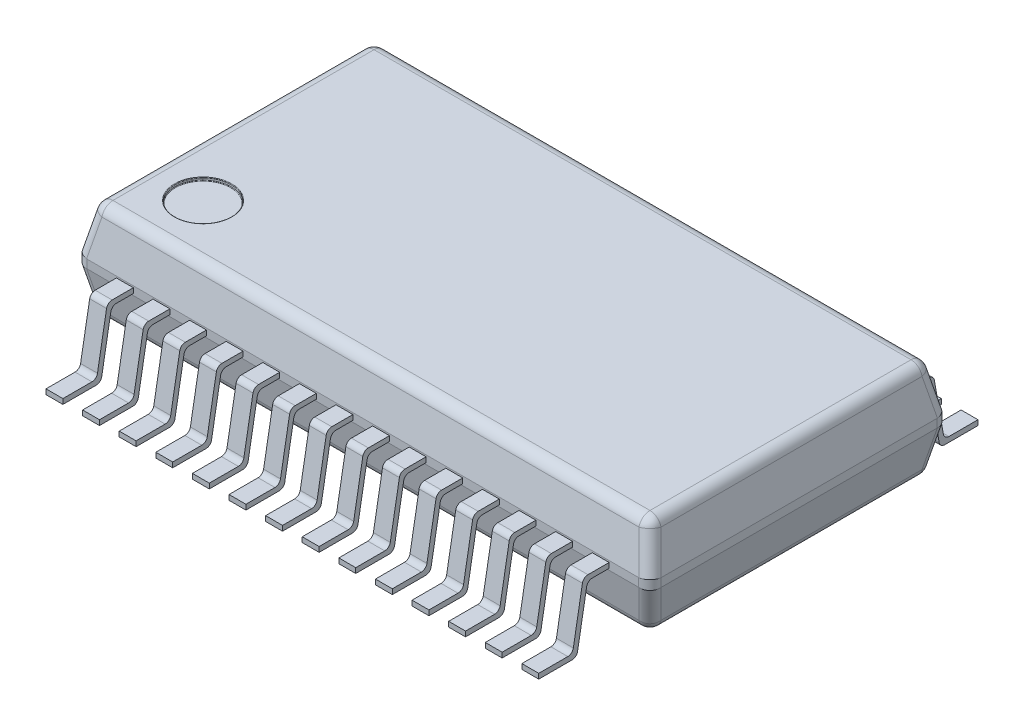
SolidWorks part; units mm, degrees
ref_plane "Front Plane" through (0, 0, 0) normal (0, 0, 1) x (1, 0, 0)
ref_plane "Top Plane" through (0, 0, 0) normal (0, 1, 0) x (1, 0, 0)
ref_plane "Right Plane" through (0, 0, 0) normal (1, 0, 0) x (0, 0, -1)
sketch "Sketch1" plane through (0, 0, 0) normal (0, 1, 0) x (1, 0, 0)
  line L1 (5.1, 2.65) -> (-5.1, 2.65)
  line L2 (5.1, 2.65) -> (5.1, -2.65)
  line L3 (5.1, -2.65) -> (-5.1, -2.65)
  line L4 (-5.1, 2.65) -> (-5.1, -2.65)
  line L5 (5.1, 2.65) -> (-5.1, -2.65) construction
  line L6 (5.1, -2.65) -> (-5.1, 2.65) construction
  point P0 (0, 0)
  dimension "D1" = 10.2
  dimension "D2" = 5.3
extrude "Boss-Extrude1" add sketch "Sketch1" along normal blind 1.75 from offset 0.25
sketch "Sketch2" plane through (5.1, 0, 0) normal (1, 0, 0) x (0, 0, -1)
  line L0 (-2.65, 1.125) -> (-3.9, 1.125) construction
  line L1 (-2.65, 2) -> (-2.65, 0.25) construction
  line L2 (-3.9, 1.125) -> (-3.9, 0) construction
  line L3 (-2.65, 1.17) -> (-3.0262, 1.17)
  line L4 (-3.1247, 1.0874) -> (-3.2859, 0.1726)
  line L5 (-3.3844, 0.09) -> (-3.9, 0.09)
  line L6 (-3.9, 0.09) -> (-3.9, 0)
  line L7 (-3.9, 0) -> (-3.3089, 0)
  line L8 (-3.2104, 0.0826) -> (-3.0491, 0.9974)
  line L9 (-2.9507, 1.08) -> (-2.65, 1.08)
  line L10 (-2.65, 1.17) -> (-2.65, 1.08)
  arc A0 (-3.2104, 0.0826) -> (-3.3089, 0) centre (-3.3089, 0.1) cw
  arc A1 (-3.2859, 0.1726) -> (-3.3844, 0.09) centre (-3.3844, 0.19) cw
  arc A2 (-2.9507, 1.08) -> (-3.0491, 0.9974) centre (-2.9507, 0.98) ccw
  arc A3 (-3.0262, 1.17) -> (-3.1247, 1.0874) centre (-3.0262, 1.07) ccw
  point P15 (-3.225, 0)
  dimension "D8" = 0.1
  dimension "D1" = 1.25
  dimension "D2" = 0.09
  dimension "D3" = 0.09
  dimension "D4" = 0.09
  dimension "D5" = 0.045
  dimension "D6" = 0.675
  dimension "D7" = 100
extrude "Boss-Extrude2" add sketch "Sketch2" against normal blind 0.3 from offset 0.725 separate body offset against normal yes
pattern_linear "LPattern1" count 14 spacing 0.65 along (-1, 0, 0) of "Boss-Extrude2"
mirror "Mirror1" about plane through (0, 0, 0) normal (0, 0, 1) of "Boss-Extrude2", "LPattern1"
chamfer "Chamfer1" distance 0.8 angle 12 4 edges at (-5.1, 2, 0) (0, 2, 2.65) (5.1, 2, 0) (0, 2, -2.65)
chamfer "Chamfer2" distance 0.8 angle 12 4 edges at (0, 0.25, 2.65) (-5.1, 0.25, 0) (0, 0.25, -2.65) (5.1, 0.25, 0)
fillet "Fillet1" radius 0.2 20 edges at (5.015, 0.65, 2.565) (5.1, 1.125, 2.65) (5.015, 1.6, 2.565) (-5.015, 0.65, 2.565) (-5.1, 1.125, 2.65) (-5.015, 1.6, 2.565) (-5.015, 0.65, -2.565) (-5.1, 1.125, -2.65) (-5.015, 1.6, -2.565) (5.015, 0.65, -2.565) (5.1, 1.125, -2.65) (5.015, 1.6, -2.565) (0, 0.25, -2.48) (-4.93, 0.25, 0) (0, 0.25, 2.48) (4.93, 0.25, 0) (-4.93, 2, 0) (0, 2, -2.48) (4.93, 2, 0) (0, 2, 2.48)
sketch "Sketch3" plane through (0, 2, 0) normal (0, 1, 0) x (1, 0, 0)
  line L0 (-4.768, -2.318) -> (4.768, -2.318) construction
  line L1 (-4.768, 2.318) -> (-4.768, -2.318) construction
  circle A0 centre (-3.968, -1.518) radius 0.5
  dimension "D1" = 1
  dimension "D2" = 0.8
  dimension "D3" = 0.8
extrude "Cut-Extrude1" cut sketch "Sketch3" against normal blind 0.05
fillet "Fillet2" radius 0.01 2 edges at (-3.968, 1.95, 2.018) (-3.968, 2, 2.018)
